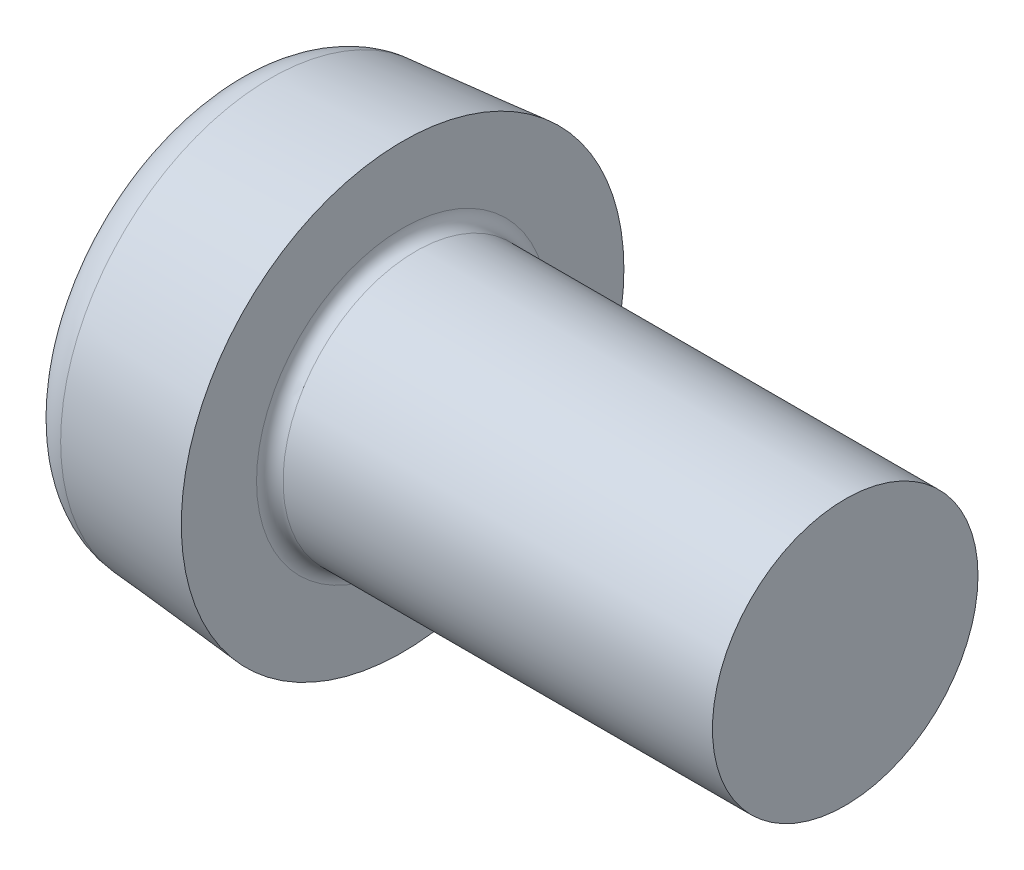
SolidWorks part; units mm, degrees
ref_plane "Front" through (0, 0, 0) normal (0, 0, 1) x (1, 0, 0)
ref_plane "Top" through (0, 0, 0) normal (0, 1, 0) x (1, 0, 0)
ref_plane "Right" through (0, 0, 0) normal (1, 0, 0) x (0, 0, -1)
sketch "Sketch1" plane through (0, 0, 0) normal (0, 0, 1) x (1, 0, 0)
  line L0 (13.9, 3) -> (5.9, 3)
  line L1 (3.9, 3.3) -> (3.9, 5)
  line L2 (3.9, 5) -> (0, 4.6588)
  line L3 (5.9, 3) -> (4.2, 3)
  line L4 (13.9, 3) -> (13.9, 0)
  line L5 (4.5158, 0) -> (-13.5157, 0) construction
  line L6 (13.9, 0) -> (0, 0)
  line L7 (0, 0) -> (0, 4.6588)
  arc A1 (3.9, 3.3) -> (4.2, 3) centre (4.2, 3.3) ccw
  dimension "r" = 0.3
  dimension "D2" = 95
  dimension "dk" = 10
  dimension "l" = 10
  dimension "a" = 2
  dimension "d" = 6
  dimension "k" = 3.9
revolve "Base" add sketch "Sketch1" angle 360 about L5
cosmetic thread "ThreadCosmetic1" [suppressed] parameters "bb"=10
sketch "Sketch6" plane through (0, 0, 0) normal (1, 0, 0) x (0, 0, -1)
  line L0 (-1.9271, 0) -> (2.0512, 0) construction
  line L1 (0, 1.8651) -> (0, -2.0207) construction
  line L2 (0.62, 0.62) -> (0.62, 3.1)
  line L3 (0.62, 3.1) -> (-0.62, 3.1)
  line L4 (-0.62, 0.62) -> (-0.62, 3.1)
  line L5 (0.62, 0.62) -> (3.1, 0.62)
  line L6 (3.1, 0.62) -> (3.1, -0.62)
  line L7 (-3.1, 0.62) -> (-3.1, -0.62)
  line L8 (-0.62, 0.62) -> (-3.1, 0.62)
  line L9 (-0.62, -0.62) -> (-3.1, -0.62)
  line L10 (0.62, -0.62) -> (3.1, -0.62)
  line L11 (-0.62, -0.62) -> (-0.62, -3.1)
  line L12 (0.62, -3.1) -> (-0.62, -3.1)
  line L13 (0.62, -0.62) -> (0.62, -3.1)
  point P16 (-3.1, 0)
  point P17 (3.1, 0)
extrude "CrossRecess" cut sketch "Sketch6" along normal blind 3.9
fillet "Fillet5" radius 0.3 4 edges at (1.95, -0.62, 0.62) (1.95, -0.62, -0.62) (1.95, 0.62, 0.62) (1.95, 0.62, -0.62)
sketch "Sketch8" [suppressed] plane through (0, 0, 0) normal (0, 0, 1) x (1, 0, 0)
  line L0 (12, 4) -> (8.2, 3.5)
  line L1 (8.2, 3.5) -> (5, 3.5)
  line L3 (50, -4) -> (50, 4) construction
  line L4 (5, -6.5) -> (5, 6.5) construction
  line L6 (5, 3.5) -> (5, 14)
  line L7 (5, 14) -> (12, 14)
  line L8 (12, 14) -> (12, 4)
  line L9 (52.4753, 0) -> (42.9594, 0) construction
  dimension "D1" = 26
  dimension "x" = 2.5
  dimension "d" = 6
  dimension "THD_MINOR" = 4.917
  dimension "b" = 38
fillet "HeadFillet" radius 1 1 edges at (0, 0, -4.6588)
draft "Draft1" type of draft neutral plane draft angle 20 faces to draft 4 face at (1.95, 0, 3.1) face at (1.95, -3.1, 0) face at (1.95, 0, -3.1) face at (1.95, 3.1, 0) neutral plane through (0, 0, 0) neutral plane normal (-1, 0, 0) parameters "D1"=20
sketch "Sketch7" plane through (0, 0, 0) normal (1, 0, 0) x (0, 0, -1)
  line L0 (-8.3217, 0) -> (7.4212, 0) construction
  line L1 (0, 7.4989) -> (0, -7.9646) construction
  line L2 (0, 0) -> (6.8599, 6.8599) construction
  line L3 (2.192, 2.192) -> (0, 1.1699)
  line L4 (0, 0) -> (-6.8599, 6.8599) construction
  line L5 (2.192, 2.192) -> (1.1699, 0)
  line L6 (2.192, -2.192) -> (0, -1.1699)
  line L7 (2.192, -2.192) -> (1.1699, 0)
  line L8 (-2.192, -2.192) -> (0, -1.1699)
  line L9 (-2.192, -2.192) -> (-1.1699, 0)
  line L10 (-2.192, 2.192) -> (0, 1.1699)
  line L11 (-2.192, 2.192) -> (-1.1699, 0)
  dimension "D2" = 20
  dimension "m" = 6.2
extrude "Cut-Extrude3" [suppressed] cut sketch "Sketch7" along normal blind 10 draft 20
sketch "Sketch10" plane through (0, 0, 0) normal (0, 0, 1) x (1, 0, 0)
  line L0 (13.9, 2.531) -> (14.1707, 3)
  line L1 (14.1707, 3) -> (14.1707, 3.5415)
  line L2 (14.1707, 3.5415) -> (13.6292, 3.5415)
  line L3 (13.6292, 3.5415) -> (13.6292, 3)
  line L4 (13.6292, 3) -> (13.9, 2.531)
  line L5 (13.9, 3) -> (5.9, 3) construction
  line L6 (13.9, 3) -> (13.9, 0) construction
  line L7 (0, 0) -> (57.111, 0) construction
  dimension "D1" = 0.5415
revolve "Cut-Revolve10" [suppressed] cut sketch "Sketch10" angle 360 about L7
pattern_linear "LPattern10" [suppressed] count 15 spacing 0.6498 along (1, 0, 0)
equation "\"D1@Sketch6\" = \"m@Sketch6\" / 5"
equation "\"D1@Sketch8\" = \"d@Sketch8\" + 20"
equation "\"D1@Sketch10\" =  ( \"d@Sketch1\" - \"THD_MINOR@ThreadCosmetic1\" )  / 2"
equation "\"D3@LPattern10\" = \"D1@Sketch10\" * 1.2"
equation "\"D1@LPattern10\" = \"bb@ThreadCosmetic1\" / \"D3@LPattern10\" "
